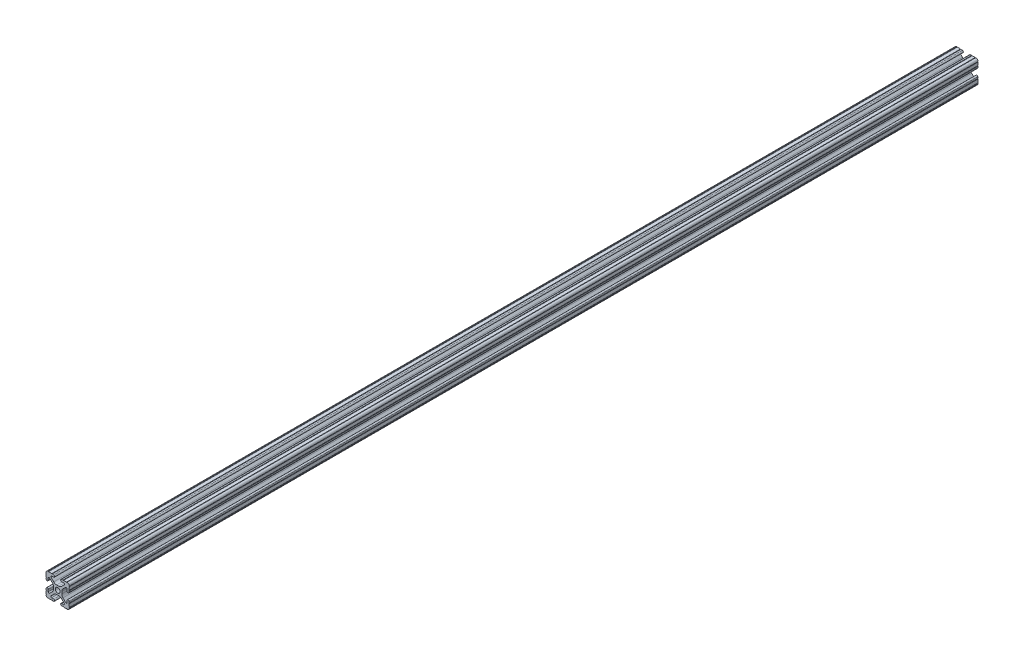
SolidWorks part; units mm, degrees
ref_plane "Front Plane" through (0, 0, 0) normal (0, 0, 1) x (1, 0, 0)
ref_plane "Top Plane" through (0, 0, 0) normal (0, 1, 0) x (1, 0, 0)
ref_plane "Right Plane" through (0, 0, 0) normal (1, 0, 0) x (0, 0, -1)
sketch "Sketch1" plane through (0, 0, 0) normal (0, 0, 1) x (1, 0, 0)
  line L0 (0, 12.7) -> (-12.7814, 12.7) construction
  line L1 (-4.5085, 0) -> (-4.5085, 2.9459)
  line L2 (-6.0437, 12.5461) -> (-10.0976, 12.6876) construction
  line L3 (-11.5616, 12.4229) -> (-4.3159, 12.1699) construction
  line L4 (-6.4364, 10.3486) -> (-6.3592, 12.5571) construction
  line L6 (-2.9459, 4.5085) -> (0, 4.5085)
  line L7 (0, 0) -> (0, 12.7) construction
  line L8 (0, 0) -> (-12.7814, 0) construction
  line L9 (0.7813, 0.7813) -> (-0.7813, -0.7813) construction
  line L10 (-2.9459, 4.5085) -> (-7.1484, 8.711)
  line L11 (-4.5085, 2.9459) -> (-8.711, 7.1484)
  line L13 (0, 0) -> (-12.7814, 12.7814) construction
  line L14 (-10.4131, 12.6987) -> (-4.3048, 12.4853)
  line L15 (-4.3048, 12.4853) -> (-4.382, 10.2769) construction
  line L16 (-4.382, 10.2769) -> (-6.4364, 10.3486)
  line L17 (-12.6987, 10.4131) -> (-12.4853, 4.3048)
  line L18 (-10.2769, 4.382) -> (-10.3486, 6.4364)
  circle A0 centre (0, 0) radius 2.6035
  arc A1 (-4.382, 10.2769) -> (-4.3048, 12.4853) centre (-4.3434, 11.3811) ccw
  arc A2 (-7.1484, 8.711) -> (-6.4364, 10.3486) centre (-6.4698, 9.3896) cw
  arc A3 (-8.711, 7.1484) -> (-10.3486, 6.4364) centre (-9.3896, 6.4698) ccw
  arc A4 (-10.2769, 4.382) -> (-12.4853, 4.3048) centre (-11.3811, 4.3434) cw
  arc A5 (-10.4131, 12.6987) -> (-12.6987, 10.4131) centre (-10.4902, 10.4902) ccw
  arc A6 (-10.4131, 12.6987) -> (-9.7821, 12.6766) centre (-10.0976, 12.6876) ccw
  arc A7 (-6.3592, 12.5571) -> (-5.7282, 12.5351) centre (-6.0437, 12.5461) ccw
  arc A8 (-12.5571, 6.3592) -> (-12.5351, 5.7282) centre (-12.5461, 6.0437) cw
  arc A9 (-12.6987, 10.4131) -> (-12.6766, 9.7821) centre (-12.6876, 10.0976) cw
  dimension "D1" = 5.207
  dimension "D5" = 14.859
  dimension "D9" = 2
  dimension "D2" = 25.4
  dimension "D12" = 0.6314
  dimension "D10" = 2.2098
  dimension "D3" = 9.017
  dimension "D4" = 9.017
  dimension "D6" = 25.4
  dimension "D7" = 6.477
  dimension "D8" = 2.2098
  dimension "D11" = 12.7
sketch "Sketch3" plane through (0, 0, 0) normal (0, 0, 1) x (1, 0, 0)
  line L0 (-2.9459, 4.5085) -> (0, 4.5085) construction
  line L1 (-2.9459, 4.5085) -> (-7.1484, 8.711) construction
  line L2 (-4.382, 10.2769) -> (-6.4364, 10.3486) construction
  line L3 (-10.4131, 12.6987) -> (-4.3048, 12.4853) construction
  line L4 (-4.5085, 0) -> (-4.5085, 2.9459) construction
  line L5 (-4.5085, 2.9459) -> (-8.711, 7.1484) construction
  line L6 (-10.2769, 4.382) -> (-10.3486, 6.4364) construction
  line L7 (-12.6987, 10.4131) -> (-12.4853, 4.3048) construction
  line L8 (-1.1153, 4.5085) -> (1.1153, 4.5085)
  line L9 (-4.2404, 5.803) -> (-7.1484, 8.711)
  line L10 (-4.382, 10.2769) -> (-6.4364, 10.3486)
  line L11 (-9.7821, 12.6766) -> (-6.3592, 12.5571)
  line L12 (-4.5085, -1.1153) -> (-4.5085, 1.1153)
  line L13 (-5.803, 4.2404) -> (-8.711, 7.1484)
  line L14 (-10.2769, 4.382) -> (-10.3486, 6.4364)
  line L15 (-12.6766, 9.7821) -> (-12.5571, 6.3592)
  line L16 (-5.7282, 12.5351) -> (-4.3048, 12.4853)
  line L17 (-12.5351, 5.7282) -> (-12.4853, 4.3048)
  line L18 (0, 0) -> (0, 12.7) construction
  line L19 (0, 0) -> (-12.7814, 0) construction
  line L20 (12.5351, 5.7282) -> (12.4853, 4.3048)
  line L21 (5.7282, 12.5351) -> (4.3048, 12.4853)
  line L22 (12.6766, 9.7821) -> (12.5571, 6.3592)
  line L23 (10.2769, 4.382) -> (10.3486, 6.4364)
  line L24 (5.803, 4.2404) -> (8.711, 7.1484)
  line L25 (4.5085, -1.1153) -> (4.5085, 1.1153)
  line L26 (9.7821, 12.6766) -> (6.3592, 12.5571)
  line L27 (4.382, 10.2769) -> (6.4364, 10.3486)
  line L28 (4.2404, 5.803) -> (7.1484, 8.711)
  line L29 (4.2404, -5.803) -> (7.1484, -8.711)
  line L30 (4.382, -10.2769) -> (6.4364, -10.3486)
  line L31 (9.7821, -12.6766) -> (6.3592, -12.5571)
  line L32 (5.803, -4.2404) -> (8.711, -7.1484)
  line L33 (10.2769, -4.382) -> (10.3486, -6.4364)
  line L34 (12.6766, -9.7821) -> (12.5571, -6.3592)
  line L35 (5.7282, -12.5351) -> (4.3048, -12.4853)
  line L36 (12.5351, -5.7282) -> (12.4853, -4.3048)
  line L37 (-12.5351, -5.7282) -> (-12.4853, -4.3048)
  line L38 (-5.7282, -12.5351) -> (-4.3048, -12.4853)
  line L39 (-12.6766, -9.7821) -> (-12.5571, -6.3592)
  line L40 (-10.2769, -4.382) -> (-10.3486, -6.4364)
  line L41 (-5.803, -4.2404) -> (-8.711, -7.1484)
  line L42 (-9.7821, -12.6766) -> (-6.3592, -12.5571)
  line L43 (-4.382, -10.2769) -> (-6.4364, -10.3486)
  line L44 (-4.2404, -5.803) -> (-7.1484, -8.711)
  line L45 (-1.1153, -4.5085) -> (1.1153, -4.5085)
  arc A0 (-10.4131, 12.6987) -> (-9.7821, 12.6766) centre (-10.0976, 12.6876) ccw construction
  arc A1 (-6.4364, 10.3486) -> (-7.1484, 8.711) centre (-6.4698, 9.3896) ccw construction
  arc A2 (-4.382, 10.2769) -> (-4.3048, 12.4853) centre (-4.3434, 11.3811) ccw construction
  arc A3 (-8.711, 7.1484) -> (-10.3486, 6.4364) centre (-9.3896, 6.4698) ccw construction
  arc A4 (-12.4853, 4.3048) -> (-10.2769, 4.382) centre (-11.3811, 4.3434) ccw construction
  arc A5 (-6.3592, 12.5571) -> (-5.7282, 12.5351) centre (-6.0437, 12.5461) ccw construction
  arc A6 (-10.4131, 12.6987) -> (-12.6987, 10.4131) centre (-10.4902, 10.4902) ccw construction
  arc A7 (-12.6766, 9.7821) -> (-12.6987, 10.4131) centre (-12.6876, 10.0976) ccw construction
  arc A8 (-12.5351, 5.7282) -> (-12.5571, 6.3592) centre (-12.5461, 6.0437) ccw construction
  arc A9 (-10.4131, 12.6987) -> (-9.7821, 12.6766) centre (-10.0976, 12.6876) ccw
  arc A10 (-6.4364, 10.3486) -> (-7.1484, 8.711) centre (-6.4698, 9.3896) ccw
  arc A11 (-4.382, 10.2769) -> (-4.3048, 12.4853) centre (-4.3434, 11.3811) ccw
  arc A12 (-8.711, 7.1484) -> (-10.3486, 6.4364) centre (-9.3896, 6.4698) ccw
  arc A13 (-12.4853, 4.3048) -> (-10.2769, 4.382) centre (-11.3811, 4.3434) ccw
  arc A14 (-6.3592, 12.5571) -> (-5.7282, 12.5351) centre (-6.0437, 12.5461) ccw
  arc A15 (-10.4131, 12.6987) -> (-12.6987, 10.4131) centre (-10.4902, 10.4902) ccw
  arc A16 (-12.6766, 9.7821) -> (-12.6987, 10.4131) centre (-12.6876, 10.0976) ccw
  arc A17 (-12.5351, 5.7282) -> (-12.5571, 6.3592) centre (-12.5461, 6.0437) ccw
  arc A18 (-1.1153, 4.5085) -> (-4.2404, 5.803) centre (-1.1153, 8.9281) cw
  arc A19 (4.5085, 1.1153) -> (5.803, 4.2404) centre (8.9281, 1.1153) cw
  arc A20 (1.1153, 4.5085) -> (4.2404, 5.803) centre (1.1153, 8.9281) ccw
  arc A21 (-4.5085, 1.1153) -> (-5.803, 4.2404) centre (-8.9281, 1.1153) ccw
  arc A22 (12.5351, 5.7282) -> (12.5571, 6.3592) centre (12.5461, 6.0437) cw
  arc A23 (12.6766, 9.7821) -> (12.6987, 10.4131) centre (12.6876, 10.0976) cw
  arc A24 (10.4131, 12.6987) -> (12.6987, 10.4131) centre (10.4902, 10.4902) cw
  arc A25 (6.3592, 12.5571) -> (5.7282, 12.5351) centre (6.0437, 12.5461) cw
  arc A26 (12.4853, 4.3048) -> (10.2769, 4.382) centre (11.3811, 4.3434) cw
  arc A27 (8.711, 7.1484) -> (10.3486, 6.4364) centre (9.3896, 6.4698) cw
  arc A28 (4.382, 10.2769) -> (4.3048, 12.4853) centre (4.3434, 11.3811) cw
  arc A29 (6.4364, 10.3486) -> (7.1484, 8.711) centre (6.4698, 9.3896) cw
  arc A30 (10.4131, 12.6987) -> (9.7821, 12.6766) centre (10.0976, 12.6876) cw
  arc A31 (10.4131, -12.6987) -> (9.7821, -12.6766) centre (10.0976, -12.6876) ccw
  arc A32 (6.4364, -10.3486) -> (7.1484, -8.711) centre (6.4698, -9.3896) ccw
  arc A33 (4.382, -10.2769) -> (4.3048, -12.4853) centre (4.3434, -11.3811) ccw
  arc A34 (8.711, -7.1484) -> (10.3486, -6.4364) centre (9.3896, -6.4698) ccw
  arc A35 (12.4853, -4.3048) -> (10.2769, -4.382) centre (11.3811, -4.3434) ccw
  arc A36 (6.3592, -12.5571) -> (5.7282, -12.5351) centre (6.0437, -12.5461) ccw
  arc A37 (10.4131, -12.6987) -> (12.6987, -10.4131) centre (10.4902, -10.4902) ccw
  arc A38 (12.6766, -9.7821) -> (12.6987, -10.4131) centre (12.6876, -10.0976) ccw
  arc A39 (12.5351, -5.7282) -> (12.5571, -6.3592) centre (12.5461, -6.0437) ccw
  arc A40 (-4.5085, -1.1153) -> (-5.803, -4.2404) centre (-8.9281, -1.1153) cw
  arc A41 (1.1153, -4.5085) -> (4.2404, -5.803) centre (1.1153, -8.9281) cw
  arc A42 (4.5085, -1.1153) -> (5.803, -4.2404) centre (8.9281, -1.1153) ccw
  arc A43 (-1.1153, -4.5085) -> (-4.2404, -5.803) centre (-1.1153, -8.9281) ccw
  arc A44 (-12.5351, -5.7282) -> (-12.5571, -6.3592) centre (-12.5461, -6.0437) cw
  arc A45 (-12.6766, -9.7821) -> (-12.6987, -10.4131) centre (-12.6876, -10.0976) cw
  arc A46 (-10.4131, -12.6987) -> (-12.6987, -10.4131) centre (-10.4902, -10.4902) cw
  arc A47 (-6.3592, -12.5571) -> (-5.7282, -12.5351) centre (-6.0437, -12.5461) cw
  arc A48 (-12.4853, -4.3048) -> (-10.2769, -4.382) centre (-11.3811, -4.3434) cw
  arc A49 (-8.711, -7.1484) -> (-10.3486, -6.4364) centre (-9.3896, -6.4698) cw
  arc A50 (-4.382, -10.2769) -> (-4.3048, -12.4853) centre (-4.3434, -11.3811) cw
  arc A51 (-6.4364, -10.3486) -> (-7.1484, -8.711) centre (-6.4698, -9.3896) cw
  arc A52 (-10.4131, -12.6987) -> (-9.7821, -12.6766) centre (-10.0976, -12.6876) cw
  circle A53 centre (0, 0) radius 2.6035 construction
  circle A54 centre (0, 0) radius 2.6035
  point P135 (4.5085, 0)
  dimension "D2" = 4.4196
extrude "Extrude1" add sketch "Sketch3" along normal mid plane 990.6
equation "\"D10@Sketch1\" = \"D8@Sketch1\""
equation "\"D11@Sketch1\" = \"D6@Sketch1\"/2"
equation "\"D12@Sketch1\" = \"D8@Sketch1\"/3.5"
equation "\"D2@Sketch3\" = \"D8@Sketch1\"*2"
